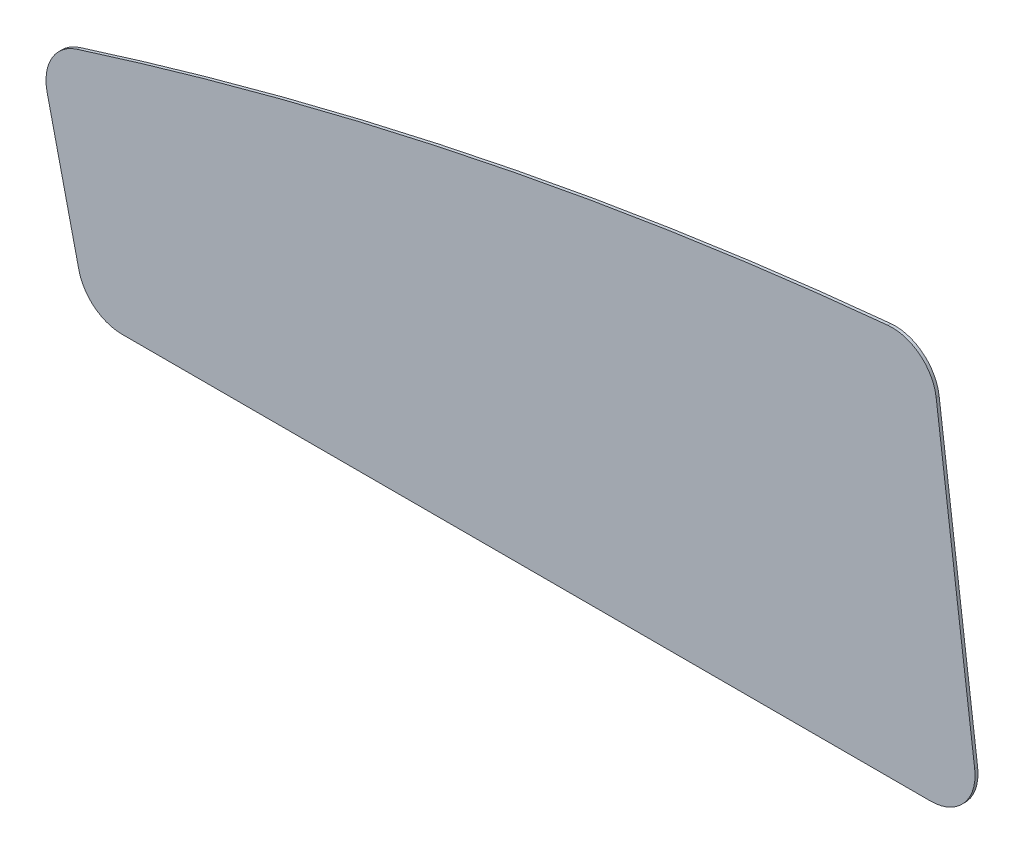
SolidWorks part; units mm, degrees
ref_plane "Plano frontal" through (0, 0, 0) normal (0, 0, 1) x (1, 0, 0)
ref_plane "Plano superior" through (0, 0, 0) normal (0, 1, 0) x (1, 0, 0)
ref_plane "Plano direito" through (0, 0, 0) normal (1, 0, 0) x (0, 0, -1)
sketch "Esboço1" plane through (0, 0, 0) normal (0, 0, 1) x (1, 0, 0)
  line L2 (94.4446, 61.6676) -> (367.7769, 61.6676)
  line L3 (382.6566, 78.5635) -> (369.642, 180.7086)
  line L5 (69.1131, 119.8406) -> (79.827, 73.3024)
  arc A0 (79.1945, 137.5034) -> (69.1131, 119.8406) centre (83.7308, 123.2058) ccw
  arc A1 (369.642, 180.7086) -> (353.3301, 193.7442) centre (354.7623, 178.8127) ccw
  arc A2 (367.7769, 61.6676) -> (382.6566, 78.5635) centre (367.7769, 76.6676) ccw
  arc A3 (79.827, 73.3024) -> (94.4446, 61.6676) centre (94.4446, 76.6676) ccw
  spline S0 degree 3 poles (79.1945, 137.5034) (169.3842, 166.1184) (260.7628, 184.8653) (353.3301, 193.7442) knots 0.031643 0.031643 0.031643 0.031643 0.681355 0.681355 0.681355 0.681355
  point P12 (349.4084, 173.6368)
  point P13 (353.6545, 85.5994)
  point P14 (98.6009, 81.0702)
extrude "Ressalto-extrusão1" add sketch "Esboço1" along normal blind 1
